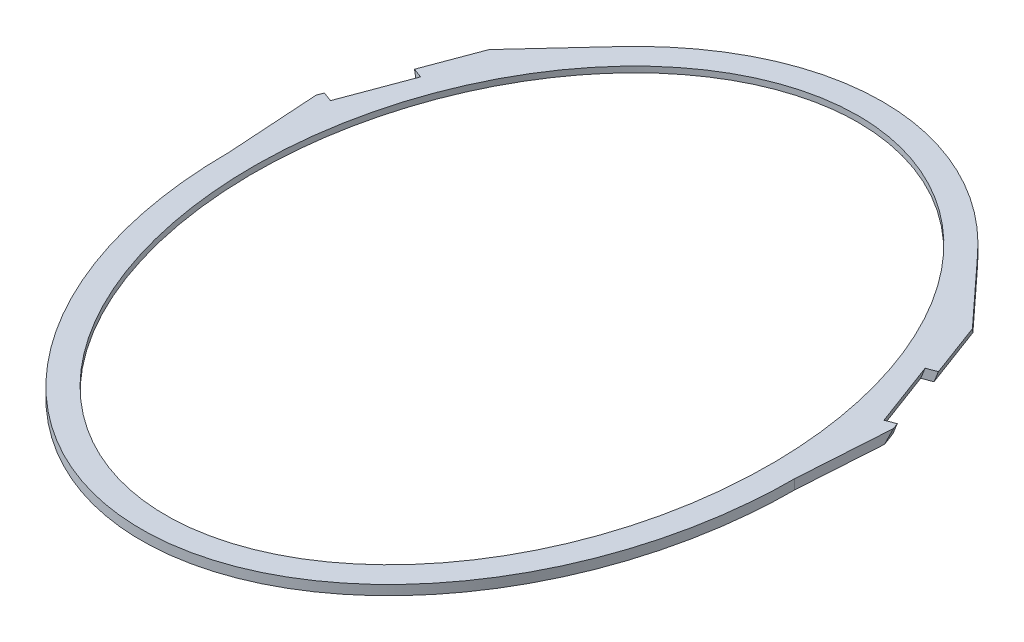
SolidWorks part; units mm, degrees
ref_plane "Front Plane" through (0, 0, 0) normal (0, 0, 1) x (1, 0, 0)
ref_plane "Top Plane" through (0, 0, 0) normal (0, 1, 0) x (1, 0, 0)
ref_plane "Right Plane" through (0, 0, 0) normal (1, 0, 0) x (0, 0, -1)
sketch "Sketch1" plane through (0, 0, 0) normal (0, 1, 0) x (1, 0, 0)
  line L0 (0, 520.2694) -> (0, -520.3963) construction
  ellipse E0 centre (0, 0) end of major axis (0, 355) minor radius 265
  ellipse E1 centre (0, 0) end of major axis (0, 380) minor radius 290
  dimension "D1" = 530
  dimension "D2" = 710
  dimension "D3" = 580
  dimension "D4" = 760
extrude "Boss-Extrude1" add sketch "Sketch1" along normal blind 10
sketch "Sketch2" plane through (0, 0, 0) normal (0, -1, 0) x (1, 0, 0)
  line L0 (0, -520.2694) -> (0, 520.3963) construction
  ellipse E0 centre (0, 0) end of major axis (0, 355) minor radius 265
  ellipse E2 centre (0, 0) end of major axis (0, 365) minor radius 275
  dimension "D1" = 10
  dimension "D2" = 10
extrude "Cut-Extrude1" cut sketch "Sketch2" against normal blind 4
sketch "Sketch4" plane through (0, 0, 0) normal (0, -1, 0) x (1, 0, 0)
  line L0 (-290, 0) -> (-295.5757, -86.6197)
  line L1 (-295.5757, -86.6197) -> (-300.753, -167.0507)
  line L3 (-241.6644, -231.1148) -> (-235.3988, -237.9079)
  line L4 (-235.3988, -237.9079) -> (-188.9895, -288.2251)
  line L5 (-241.6644, -231.1148) -> (-300.753, -167.0507)
  line L6 (-235.3988, -237.9079) -> (-188.9895, -288.2251) construction
  line L8 (-188.9895, -288.2251) -> (-243.259, -170.233)
  line L9 (0, 0) -> (0, -412.1896) construction
  line L10 (-243.259, -170.233) -> (-265.308, -122.2944)
  line L11 (-265.308, -122.2944) -> (-290, 0)
  ellipse E1 centre (0, 0) end of major axis (0, -380) minor radius 290 construction
  ellipse E2 centre (0, 0) end of major axis (0, 365) minor radius 275 construction
extrude "Boss-Extrude2" add sketch "Sketch4" against normal blind 10
ref_plane "Plane1" through (-256.4857, -95.6951, -95.6951) normal (-0.8844, -0.33, -0.33) x (-0.3092, -0.1154, 0.944)
sketch "Sketch5" plane through (-256.4857, -95.6951, -95.6951) normal (-0.8844, -0.33, -0.33) x (-0.3092, -0.1154, 0.944)
  line L1 (-239.4181, 192.9721) -> (70.1119, 192.9721)
  line L2 (-239.4181, 192.9721) -> (-239.4181, 21.3)
  line L3 (-239.4181, 21.3) -> (70.1119, 21.3)
  line L4 (70.1119, 192.9721) -> (70.1119, 21.3)
extrude "Cut-Extrude2" cut sketch "Sketch5" along normal through all
sketch "Sketch6" plane through (-256.4857, -95.6951, -95.6951) normal (-0.8844, -0.33, -0.33) x (-0.3092, -0.1154, 0.944)
  line L0 (-4.7884, 101.5492) -> (-6.0828, 112.0632)
  line L1 (-143.4551, 84.477) -> (9.6139, 103.3224) construction
  line L2 (-136.2589, 96.0363) -> (0.5793, 112.8834) construction
  line L3 (-3.4939, 91.0353) -> (-4.7884, 101.5492) construction
  line L4 (-76.0768, 92.7724) -> (-77.3713, 103.2864)
  line L5 (-76.0768, 92.7724) -> (-74.7824, 82.2584) construction
  line L6 (-4.7884, 101.5492) -> (-3.4939, 91.0353)
  line L7 (-3.4939, 91.0353) -> (-74.7824, 82.2584)
  line L8 (-74.7824, 82.2584) -> (-76.0768, 92.7724)
  line L9 (-77.3713, 103.2864) -> (-78.4519, 112.0632)
  line L10 (-78.4519, 112.0632) -> (-7.1634, 120.8401)
  line L11 (-7.1634, 120.8401) -> (-6.0828, 112.0632)
extrude "Cut-Extrude3" cut sketch "Sketch6" against normal blind 10
mirror "Mirror1" about plane through (0, 0, 0) normal (1, 0, 0) of "Cut-Extrude3", "Cut-Extrude2", "Boss-Extrude2"
